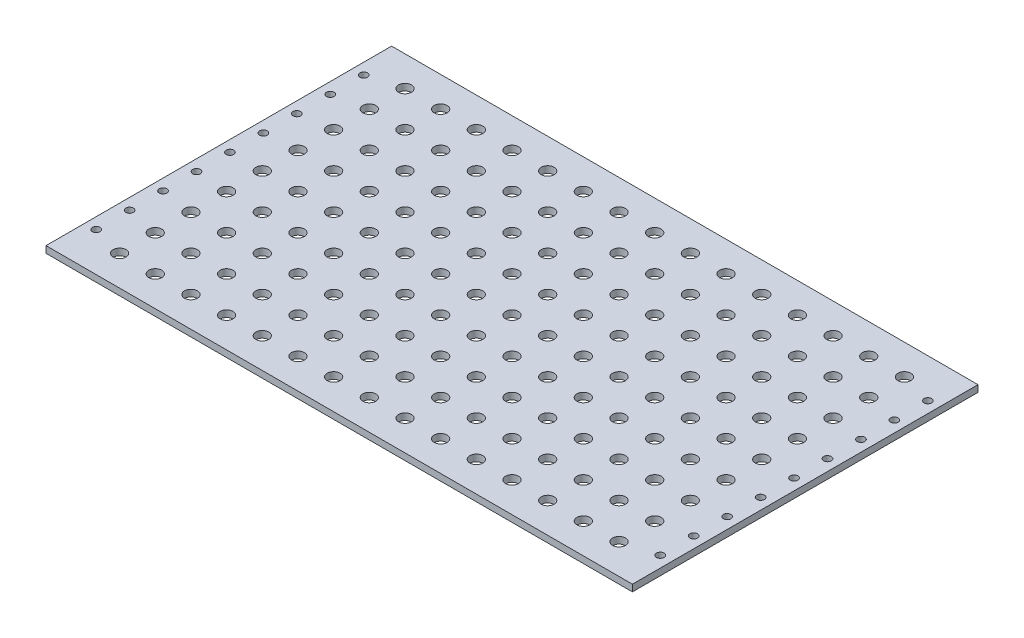
SolidWorks part; units mm, degrees
ref_plane "Front" through (0, 0, 0) normal (0, 0, 1) x (1, 0, 0)
ref_plane "Top" through (0, 0, 0) normal (0, 1, 0) x (1, 0, 0)
ref_plane "Right" through (0, 0, 0) normal (1, 0, 0) x (0, 0, -1)
sketch "Croquis1" plane through (0, 0, 0) normal (0, 1, 0) x (1, 0, 0)
  line L1 (-131.5, 77.5) -> (131.5, 77.5)
  line L2 (-131.5, 77.5) -> (-131.5, -77.5)
  line L3 (-131.5, -77.5) -> (131.5, -77.5)
  line L4 (131.5, 77.5) -> (131.5, -77.5)
  line L5 (-131.5, 77.5) -> (131.5, -77.5) construction
  line L6 (-131.5, -77.5) -> (131.5, 77.5) construction
  point P0 (0, 0)
  dimension "D1" = 263
  dimension "D2" = 155
extrude "Saliente-Extruir1" add sketch "Croquis1" along normal blind 3
sketch "Croquis2" plane through (0, 0, 0) normal (0, -1, 0) x (1, 0, 0)
  point P0 (0, 0)
hole_wizard "Taladro de margen para M51" positions "Croquis3" profile "Croquis4" hole size "M5" standard "DIN" end condition through all
sketch "Croquis3" plane through (0, 0, 0) normal (0, -1, 0) x (-1, 0, 0)
  point P0 (0, 0)
sketch "Croquis4" plane through (0, 0, 0) normal (1, 0, 0) x (0, 0, -1)
  line L0 (0, 0) -> (0, 3)
  line L1 (0, 3) -> (2.9, 3)
  line L2 (2.9, 3) -> (2.9, 0)
  line L5 (2.9, 0) -> (0, 0)
  line L11 (0, -6.35) -> (0, 107.95) construction
  dimension "Diámetro de taladro hasta el siguiente" = 5.8
  dimension "Profundidad de taladro hasta el siguiente" = 3
pattern_linear "MatrizL1" count 8 spacing 16 along (1, 0, 0) count 5 spacing 16 along (0, 0, 1) of "Taladro de margen para M51"
mirror "Simetría1" about plane through (0, 0, 0) normal (1, 0, 0) of "MatrizL1"
mirror "Simetría2" about plane through (0, 0, 0) normal (0, 0, 1) of "Simetría1", "MatrizL1"
sketch "Croquis5" plane through (0, 0, 0) normal (0, -1, 0) x (1, 0, 0)
  line L0 (126.5, -60) -> (126.5, 60) construction
  line L2 (131.5, 77.5) -> (131.5, -77.5) construction
  point P2 (126.5, -45)
  point P3 (126.5, -30)
  point P4 (126.5, -15)
  point P5 (126.5, 0)
  point P6 (126.5, 15)
  point P8 (126.5, 30)
  point P9 (126.5, 45)
  point P10 (126.5, 60)
  point P12 (126.5, -60)
  point P15 (131.5, 0)
  dimension "D1" = 5
  dimension "D3" = 9
hole_wizard "Taladro de margen para M31" positions "Croquis6" profile "Croquis7" hole size "M3" standard "DIN" end condition through all
sketch "Croquis6" plane through (0, 0, 0) normal (0, -1, 0) x (-1, 0, 0)
  point P34 (-126.5, 60)
  point P37 (-126.5, 45)
  point P40 (-126.5, 30)
  point P43 (-126.5, 15)
  point P46 (-126.5, 0)
  point P49 (-126.5, -15)
  point P52 (-126.5, -30)
  point P55 (-126.5, -45)
  point P58 (-126.5, -60)
sketch "Croquis7" plane through (126.5, 0, -60) normal (1, 0, 0) x (0, 0, -1)
  line L0 (0, 0) -> (0, 3)
  line L1 (0, 3) -> (1.7, 3)
  line L2 (1.7, 3) -> (1.7, 0)
  line L5 (1.7, 0) -> (0, 0)
  line L11 (0, -6.35) -> (0, 107.95) construction
  dimension "Diámetro de taladro hasta el siguiente" = 3.4
  dimension "Profundidad de taladro hasta el siguiente" = 3
mirror "Simetría3" about plane through (0, 0, 0) normal (1, 0, 0) of "Taladro de margen para M31"
